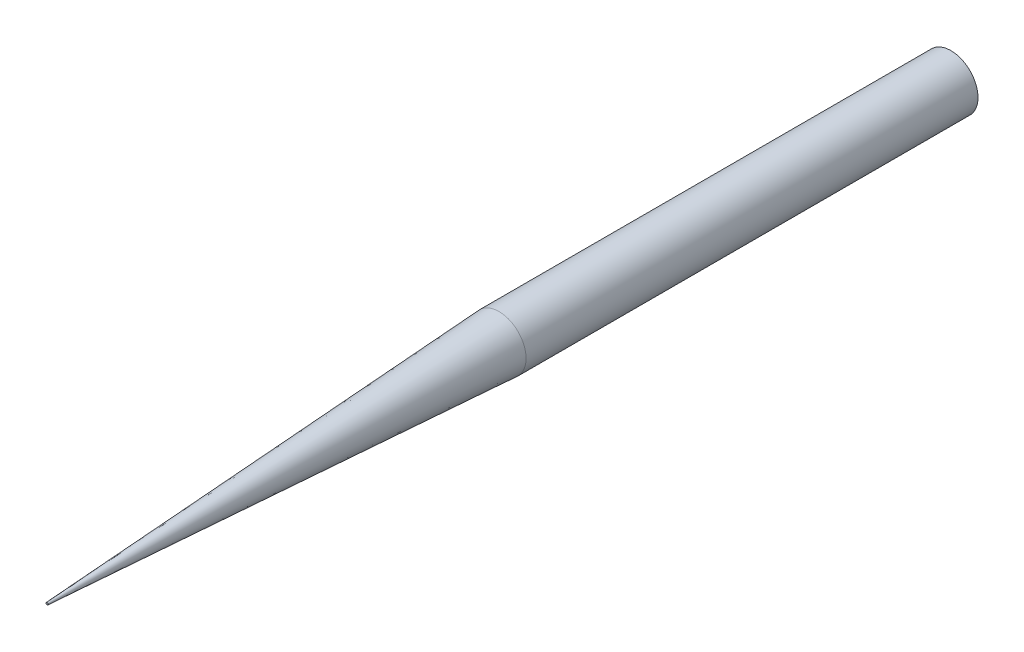
SolidWorks part; units mm, degrees
ref_plane "Front" through (0, 0, 0) normal (0, 0, 1) x (1, 0, 0)
ref_plane "Top" through (0, 0, 0) normal (0, 1, 0) x (1, 0, 0)
ref_plane "Right" through (0, 0, 0) normal (1, 0, 0) x (0, 0, -1)
sketch "Sketch1" plane through (0, 0, 0) normal (0, 0, 1) x (1, 0, 0)
  circle A0 centre (0, 0) radius 1.5
  dimension "D1" = 3
extrude "Extrude1" add sketch "Sketch1" along normal blind 50
chamfer "Chamfer1" distance 25 angle 3.3 1 edges at (1.5, 0, 50)
